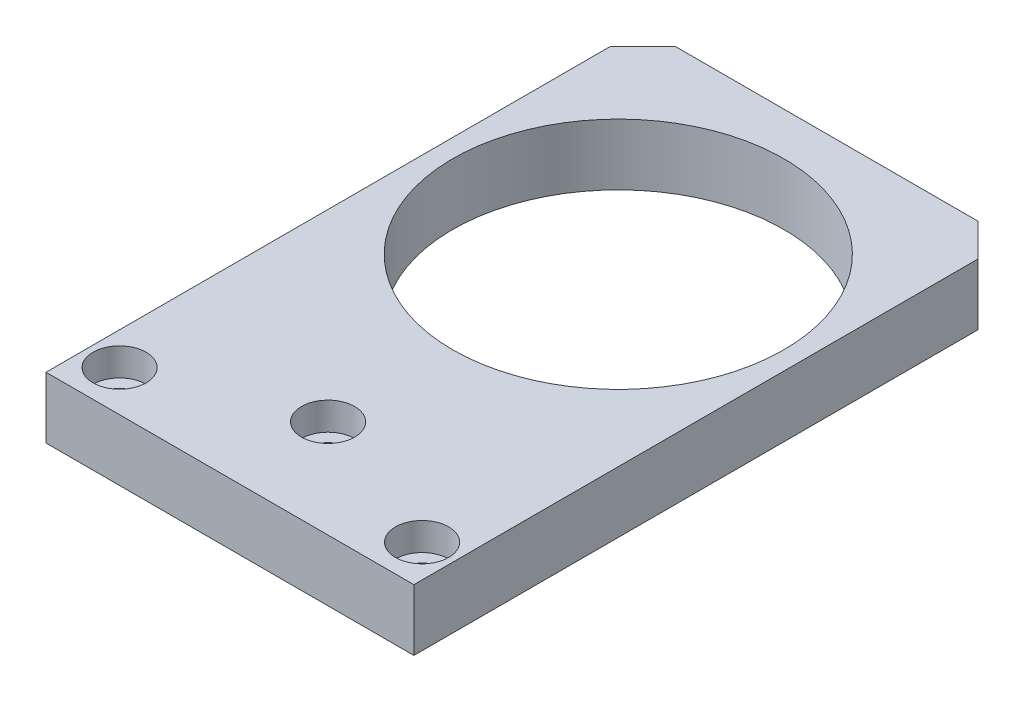
SolidWorks part; units mm, degrees
ref_plane "Front Plane" through (0, 0, 0) normal (0, 0, 1) x (1, 0, 0)
ref_plane "Top Plane" through (0, 0, 0) normal (0, 1, 0) x (1, 0, 0)
ref_plane "Right Plane" through (0, 0, 0) normal (1, 0, 0) x (0, 0, -1)
sketch "Sketch1" plane through (0, 0, 0) normal (0, 1, 0) x (1, 0, 0)
  line L1 (-22.5, 0) -> (22.5, 0)
  line L2 (-22.5, 0) -> (-22.5, 73)
  line L3 (-22.5, 73) -> (22.5, 73)
  line L4 (22.5, 0) -> (22.5, 73)
  circle A0 centre (0, 47.5) radius 20.25
  point P7 (0, 0)
  dimension "D3" = 47.5
  dimension "D4" = 40.5
  dimension "D1" = 45
  dimension "D2" = 73
extrude "Boss-Extrude1" add sketch "Sketch1" along normal blind 7.5
cosmetic thread "Cosmetic Thread1" parameters "D2"=41
chamfer "Chamfer1" distance 4 angle 45 2 edges at (-22.5, 3.75, -73) (22.5, 3.75, -73)
hole_wizard "CBORE for M3 Hex Socket Head Cap Screw1" positions "Sketch2" profile "Sketch3" counterbore size "M3" standard "DIN" end condition up to next
sketch "Sketch2" plane through (0, 7.5, 0) normal (0, 1, 0) x (1, 0, 0)
  line L0 (-22.5, 0) -> (22.5, 0) construction
  point P0 (-18.5, 5)
  point P2 (0, 12)
  point P4 (18.5, 5)
  point P9 (0, 0)
  point P11 (0, 0)
  dimension "D1" = 5
  dimension "D2" = 7
  dimension "D3" = 18.5
  dimension "D4" = 18.5
sketch "Sketch3" plane through (-18.5, 7.5, -5) normal (1, 0, 0) x (0, 0, 1)
  line L0 (0, 0) -> (0, 7.5)
  line L1 (0, 7.5) -> (1.7, 7.5)
  line L3 (1.7, 7.5) -> (1.7, 3.4)
  line L4 (1.7, 3.4) -> (3.25, 3.4)
  line L5 (3.25, 3.4) -> (3.25, 0)
  line L7 (3.25, 0) -> (0, 0)
  line L11 (0, -6.35) -> (0, 107.95) construction
  dimension "Thru Hole Dia." = 3.4
  dimension "Thru Hole Depth" = 7.5
  dimension "C'Bore Dia." = 6.5
  dimension "C'Bore Depth" = 3.4
